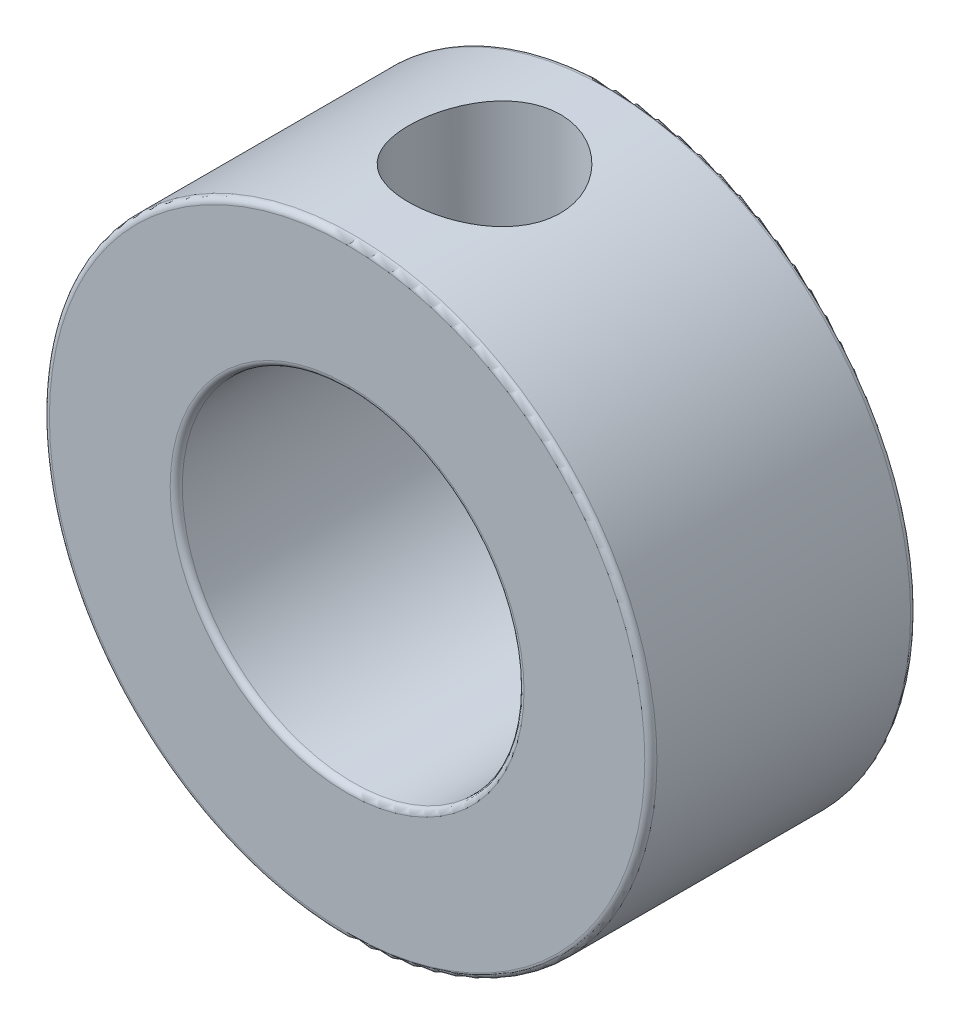
SolidWorks part; units mm, degrees
material "Alloy Steel"
ref_plane "Front Plane" through (0, 0, 0) normal (0, 0, 1) x (1, 0, 0)
ref_plane "Top Plane" through (0, 0, 0) normal (0, 1, 0) x (1, 0, 0)
ref_plane "Right Plane" through (0, 0, 0) normal (1, 0, 0) x (0, 0, -1)
sketch "Sketch1" plane through (0, 0, 0) normal (0, 0, 1) x (1, 0, 0)
  circle A0 centre (0, 0) radius 12.7
  circle A1 centre (0, 0) radius 7.1438
  dimension "D1" = 25.4
  dimension "D2" = 14.2875
extrude "Boss-Extrude1" add sketch "Sketch1" along normal blind 11.1125
fillet "Fillet1" radius 0.254 4 edges at (7.1438, 0, 0) (12.7, 0, 0) (12.7, 0, 11.1125) (7.1438, 0, 11.1125)
hole_wizard "1/4 (0.25) Diameter Hole1" positions "3DSketch1" profile "Sketch3" hole size "1/4" standard "ANSI Inch"
sketch3d "3DSketch1"
  point P0 (-0.0171, 12.7, 5.3511)
sketch "Sketch3" plane through (-0.0171, 12.7, 5.3511) normal (0, 0, 1) x (-1, -0.0013, 0)
  line L0 (0, 0) -> (0, 12.8297)
  line L1 (0, 12.8297) -> (3.175, 10.922)
  line L2 (3.175, 10.922) -> (3.175, 0)
  line L5 (3.175, 0) -> (0, 0)
  line L10 (0, 12.8297) -> (-3.175, 10.922) construction
  line L11 (0, -6.35) -> (0, 107.95) construction
  dimension "Hole Dia." = 6.35
  dimension "Hole Depth" = 10.922
  dimension "Drill Angle" = 118
